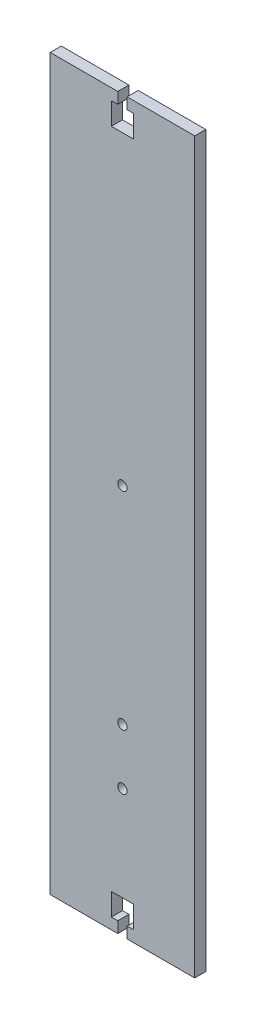
SolidWorks part; units mm, degrees
ref_plane "Front Plane" through (0, 0, 0) normal (0, 0, 1) x (1, 0, 0)
ref_plane "Top Plane" through (0, 0, 0) normal (0, 1, 0) x (1, 0, 0)
ref_plane "Right Plane" through (0, 0, 0) normal (1, 0, 0) x (0, 0, -1)
sketch "Sketch1" plane through (0, 0, 0) normal (0, 0, 1) x (1, 0, 0)
  line L1 (32.498, -164) -> (-32.498, -164)
  line L2 (32.498, -164) -> (32.498, 164)
  line L3 (32.498, 164) -> (-32.498, 164)
  line L4 (-32.498, -164) -> (-32.498, 164)
  line L5 (32.498, -164) -> (-32.498, 164) construction
  line L6 (32.498, 164) -> (-32.498, -164) construction
  point P0 (0, 0)
  dimension "D1" = 328
  dimension "D2" = 64.996
extrude "Boss-Extrude1" add sketch "Sketch1" along normal blind 5
sketch "Sketch2" plane through (0, 0, 5) normal (0, 0, 1) x (1, 0, 0)
  line L2 (-32.498, 164) -> (-32.498, -164) construction
  line L3 (-32.498, -81.5) -> (32.498, -81.5) construction
  line L4 (32.498, -164) -> (32.498, 164) construction
  circle A0 centre (0, -81.5) radius 2.1
  dimension "D1" = 4.2
extrude "Cut-Extrude1" cut sketch "Sketch2" against normal blind 10
sketch "Sketch3" plane through (0, 0, 5) normal (0, 0, 1) x (1, 0, 0)
  line L0 (0, 164) -> (0, 143.5477) construction
  line L1 (32.498, 164) -> (-32.498, 164) construction
  line L2 (-32.498, 0) -> (-5.8244, 0) construction
  line L3 (-32.498, 164) -> (-32.498, -164) construction
  line L4 (-2.1, 164) -> (2.1, 164)
  line L5 (2.1, 164) -> (2.1, 159)
  line L6 (2.1, 159) -> (5, 159)
  line L7 (5, 159) -> (5, 149)
  line L8 (5, 149) -> (-5, 149)
  line L9 (-5, 159) -> (-5, 149)
  line L10 (-2.1, 159) -> (-5, 159)
  line L11 (-2.1, 164) -> (-2.1, 159)
  line L12 (0, -164) -> (0, -143.5477) construction
  line L13 (-2.1, -164) -> (-2.1, -159)
  line L14 (-2.1, -159) -> (-5, -159)
  line L15 (-5, -159) -> (-5, -149)
  line L16 (5, -149) -> (-5, -149)
  line L17 (5, -159) -> (5, -149)
  line L18 (2.1, -159) -> (5, -159)
  line L19 (2.1, -164) -> (2.1, -159)
  line L20 (-2.1, -164) -> (2.1, -164)
  point P15 (0, 149)
  point P28 (0, -149)
  dimension "D1" = 2.1
  dimension "D2" = 5
  dimension "D3" = 5
  dimension "D4" = 10
extrude "Cut-Extrude2" cut sketch "Sketch3" against normal blind 10
sketch "Sketch4" plane through (0, 0, 5) normal (0, 0, 1) x (1, 0, 0)
  line L2 (32.498, -164) -> (32.498, 164) construction
  line L3 (32.498, -106.5) -> (-32.498, -106.5) construction
  line L4 (-32.498, 164) -> (-32.498, -164) construction
  circle A0 centre (0, -106.5) radius 2.1
  dimension "D1" = 4.2
extrude "Cut-Extrude3" cut sketch "Sketch4" against normal blind 5
sketch "Sketch5" plane through (0, 0, 5) normal (0, 0, 1) x (1, 0, 0)
  line L0 (-32.498, 11.5) -> (32.498, 11.5) construction
  line L1 (-32.498, 164) -> (-32.498, -164) construction
  line L2 (32.498, -164) -> (32.498, 164) construction
  line L3 (-41.6341, 14) -> (-33.883, 14) construction
  circle A0 centre (0, 11.5) radius 2.1
  dimension "D2" = 4.2
  dimension "D1" = 2.5
extrude "Cut-Extrude4" cut sketch "Sketch5" against normal blind 5
